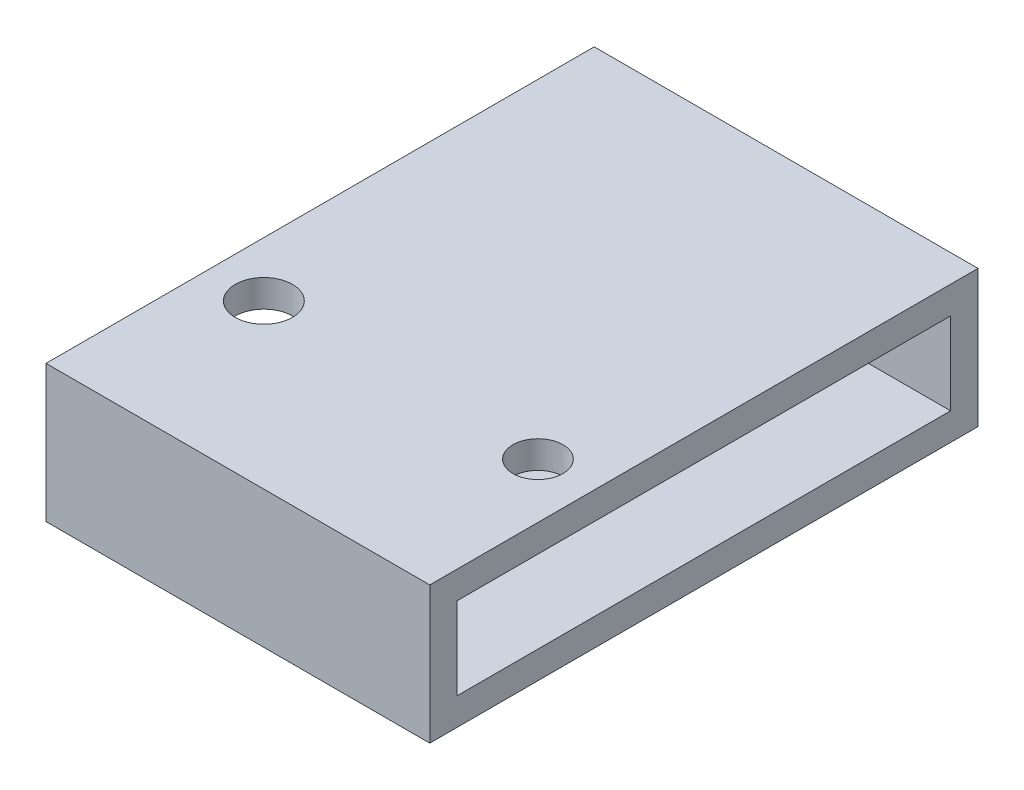
SolidWorks part; units mm, degrees
ref_plane "Front Plane" through (0, 0, 0) normal (0, 0, 1) x (1, 0, 0)
ref_plane "Top Plane" through (0, 0, 0) normal (0, 1, 0) x (1, 0, 0)
ref_plane "Right Plane" through (0, 0, 0) normal (1, 0, 0) x (0, 0, -1)
sketch "Sketch2" plane through (0, 0, 0) normal (0, 1, 0) x (1, 0, 0)
  line L1 (0, 0) -> (17.78, 0)
  line L2 (0, 0) -> (0, 25.4)
  line L3 (0, 25.4) -> (17.78, 25.4)
  line L4 (17.78, 0) -> (17.78, 25.4)
extrude "Boss-Extrude1" add sketch "Sketch2" along normal blind 6.35
sketch "Sketch3" plane through (0, 6.35, 0) normal (0, 1, 0) x (1, 0, 0)
  line L0 (3.7681, 7.5529) -> (16.4681, 7.5529) construction
  line L1 (8.89, 0) -> (8.89, 25.4) construction
  line L2 (0, 0) -> (17.78, 0) construction
  line L3 (17.78, 25.4) -> (0, 25.4) construction
  line L4 (0, 25.4) -> (0, 0) construction
  line L5 (17.78, 0) -> (17.78, 25.4) construction
  circle A0 centre (2.54, 7.5529) radius 1.3261
  circle A1 centre (15.24, 7.5529) radius 1.1592
  dimension "D1" = 12.7
  dimension "D2" = 2.54
  dimension "D3" = 2.54
extrude "Cut-Extrude2" cut sketch "Sketch3" against normal blind 3.81
sketch "Sketch4" plane through (17.78, 0, 0) normal (1, 0, 0) x (0, 0, -1)
  line L14 (24.13, 1.27) -> (24.13, 5.08)
  line L15 (1.27, 1.27) -> (24.13, 1.27)
  line L16 (1.27, 5.08) -> (1.27, 1.27)
  line L17 (24.13, 5.08) -> (1.27, 5.08)
  line L18 (24.13, 1.27) -> (24.13, 5.08)
  line L19 (1.27, 1.27) -> (24.13, 1.27)
  line L20 (1.27, 5.08) -> (1.27, 1.27)
  line L21 (24.13, 5.08) -> (1.27, 5.08)
  dimension "D1" = 1.27
extrude "Cut-Extrude3" cut sketch "Sketch4" against normal up to next contours L18 L21 L20 L19
sketch "Sketch5" plane through (0, 6.35, 0) normal (0, 1, 0) x (1, 0, 0)
